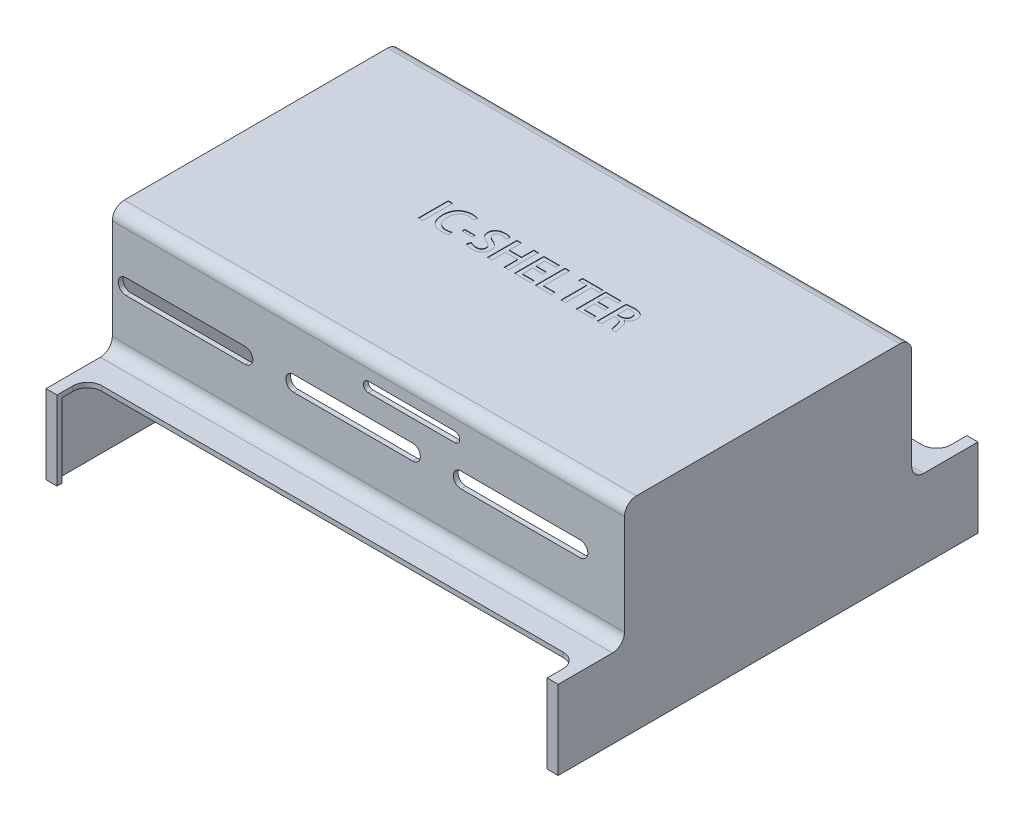
SolidWorks part; units mm, degrees
ref_plane "Alzado" through (0, 0, 0) normal (0, 0, 1) x (1, 0, 0)
ref_plane "Planta" through (0, 0, 0) normal (0, 1, 0) x (1, 0, 0)
ref_plane "Vista lateral" through (0, 0, 0) normal (1, 0, 0) x (0, 0, -1)
sketch "Sketch1" plane through (0, 0, 0) normal (1, 0, 0) x (0, 0, -1)
  line L0 (-43.85, 0) -> (-43.85, 16.5)
  line L1 (-43.85, 16.5) -> (-30, 16.5)
  line L2 (-30, 16.5) -> (-30, 42.4286)
  line L3 (30, 42.4286) -> (-30, 42.4286)
  line L5 (0, 0) -> (0, 49.86) construction
  line L8 (30, 16.5) -> (30, 42.4286)
  line L9 (43.85, 16.5) -> (30, 16.5)
  line L10 (43.85, 0) -> (43.85, 16.5)
  line L11 (-43.85, 0) -> (43.85, 0)
  dimension "D1" = 87.7
  dimension "D2" = 16.5
  dimension "D5" = 60
  dimension "D6" = 42.4286
extrude "Boss-Extrude1" add sketch "Sketch1" along normal mid plane 107
shell "Shell4" thickness 1
fillet "Fillet2" radius 2.5 1 edges at (0, 42.4286, 30)
fillet "Fillet3" radius 2.5 1 edges at (0, 16.5, 30)
fillet "Fillet4" radius 2.5 1 edges at (0, 42.4286, -30)
fillet "Fillet5" radius 2.5 1 edges at (0, 16.5, -30)
sketch "Sketch16" plane through (0, 0, 30) normal (0, 0, 1) x (1, 0, 0)
  line L3 (-50.6462, 31.081) -> (-25.7697, 31.081)
  line L4 (-25.7697, 27.8476) -> (-50.6462, 27.8476)
  arc A0 (-25.7697, 31.081) -> (-25.7697, 27.8476) centre (-25.7697, 29.4643) cw
  arc A1 (-50.6462, 27.8476) -> (-50.6462, 31.081) centre (-50.6462, 29.4643) cw
extrude "Cut-Extrude9" cut sketch "Sketch16" against normal through all
pattern_linear "LPattern4" count 3 spacing 35 along (1, 0, 0) of "Cut-Extrude9"
sketch "Sketch17" plane through (0, 41.4286, 0) normal (0, -1, 0) x (1, 0, 0)
  line L1 (-52.5, -29) -> (52.5, -29)
  line L2 (-52.5, -29) -> (-52.5, 29)
  line L3 (-52.5, 29) -> (52.5, 29)
  line L4 (52.5, -29) -> (52.5, 29)
  line L5 (-52.5, -29) -> (52.5, 29) construction
  line L6 (-52.5, 29) -> (52.5, -29) construction
  point P0 (0, 0)
extrude "Boss-Extrude2" add sketch "Sketch17" along normal blind 2
sketch "Sketch15" plane through (0, 0, -30) normal (0, 0, -1) x (-1, 0, 0)
  line L0 (0, 37.6672) -> (-18.032, 37.6672)
  line L1 (-18.032, 35.5765) -> (0, 35.5765)
  arc A0 (-18.032, 37.6672) -> (-18.032, 35.5765) centre (-18.032, 36.6219) ccw
  arc A1 (0, 35.5765) -> (0, 37.6672) centre (0, 36.6219) ccw
extrude "Cut-Extrude8" cut sketch "Sketch15" against normal through all
sketch "Sketch19" plane through (0, 16.5, 0) normal (0, 1, 0) x (1, 0, 0)
  line L4 (-48.19, -37.5) -> (48.19, -37.5)
  line L5 (53.5, -43.85) -> (-53.5, -43.85) construction
  line L6 (-51.19, -43.85) -> (-51.19, -40.5)
  line L7 (53.5, -32.5) -> (-53.5, -32.5) construction
  line L9 (51.19, -43.85) -> (51.19, -40.5)
  line L11 (-51.19, -43.85) -> (51.19, -43.85)
  arc A4 (51.19, -40.5) -> (48.19, -37.5) centre (48.19, -40.5) ccw
  arc A5 (-51.19, -40.5) -> (-48.19, -37.5) centre (-48.19, -40.5) cw
  point P10 (53.5, -32.5)
  point P13 (-53.5, -32.5)
  point P18 (51.19, -32.5)
  point P21 (-51.19, -32.5)
  dimension "D1" = 3
extrude "Cut-Extrude15" cut sketch "Sketch19" against normal through all
mirror "Mirror3" about plane through (0, 0, 0) normal (0, 0, 1) of "Cut-Extrude15"
sketch "Sketch21" plane through (0, 42.4286, 0) normal (0, 1, 0) x (1, 0, 0)
  text T0 " IC-SHELTER" font "@Adobe Heiti Std R" height in points 20
extrude "Cut-Extrude17" cut sketch "Sketch21" against normal blind 0.1
